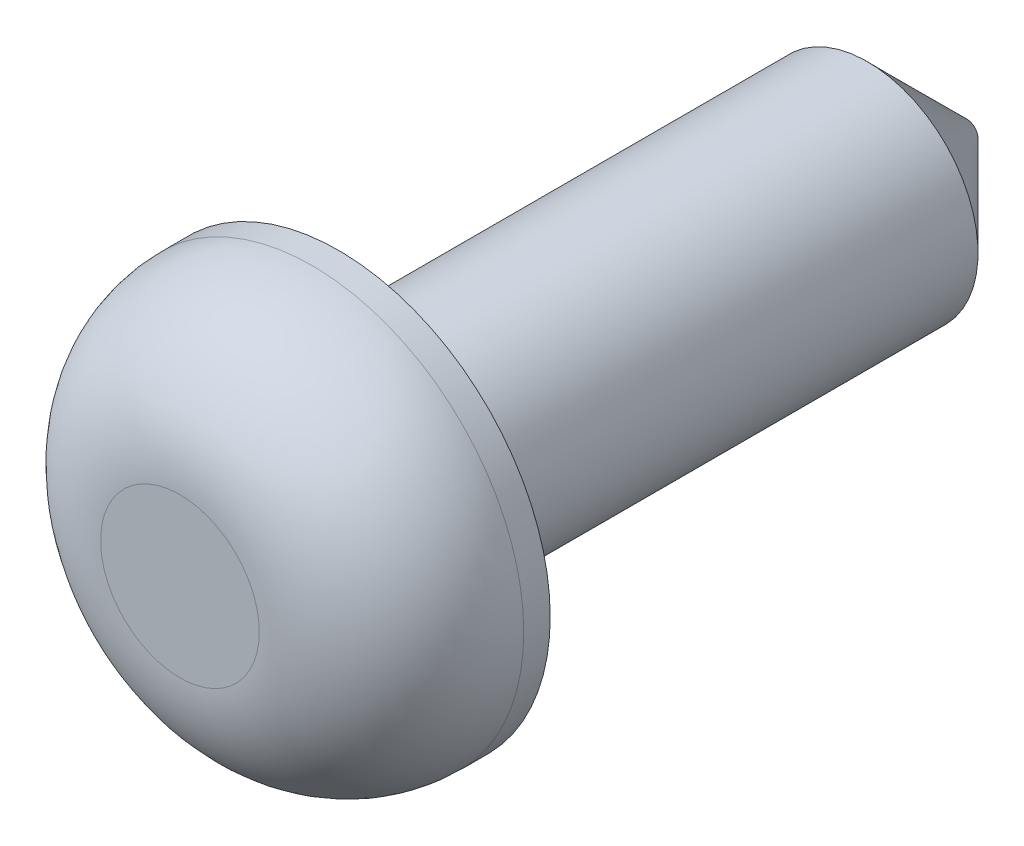
SolidWorks part; units mm, degrees
material "Zinc AC43A (Zn-4Al-2.5Cu-0.04Mg; Number 2 Die Casting Alloy; Zamak 2), Die Cast"
ref_plane "Front Plane" through (0, 0, 0) normal (0, 0, 1) x (1, 0, 0)
ref_plane "Top Plane" through (0, 0, 0) normal (0, 1, 0) x (1, 0, 0)
ref_plane "Right Plane" through (0, 0, 0) normal (1, 0, 0) x (0, 0, -1)
sketch "Sketch1" plane through (0, 0, 0) normal (0, 0, 1) x (1, 0, 0)
  circle A0 centre (0, 0) radius 4.064
  dimension "D1" = 8.128
extrude "Boss-Extrude1" add sketch "Sketch1" along normal blind 3.048
sketch "Sketch2" plane through (0, 0, 0) normal (0, 0, -1) x (-1, 0, 0)
  circle A0 centre (0, 0) radius 2.1209
  dimension "D1" = 4.2418
extrude "Boss-Extrude2" add sketch "Sketch2" along normal blind 12.065
chamfer "Chamfer1" distance 1.905 1 edges at (-2.1209, 0, -12.065)
fillet "Fillet1" radius 2.54 1 edges at (4.064, 0, 3.048)
